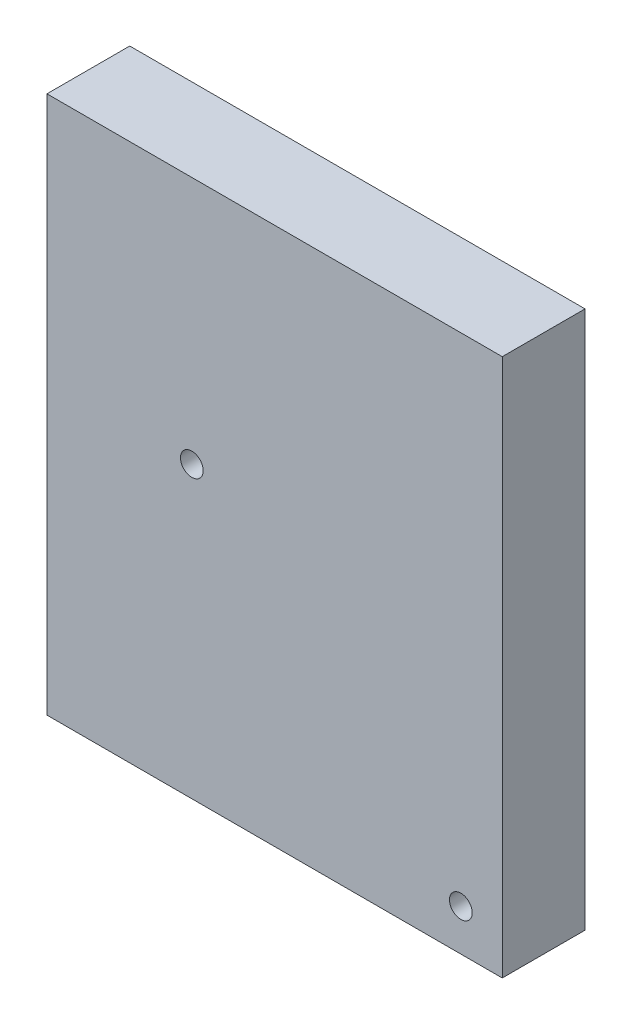
SolidWorks part; units mm, degrees
ref_plane "Front Plane" through (0, 0, 0) normal (0, 0, 1) x (1, 0, 0)
ref_plane "Top Plane" through (0, 0, 0) normal (0, 1, 0) x (1, 0, 0)
ref_plane "Right Plane" through (0, 0, 0) normal (1, 0, 0) x (0, 0, -1)
sketch "Sketch1" plane through (0, 0, 0) normal (0, 0, 1) x (1, 0, 0)
  line L1 (-27.94, -33.02) -> (27.94, -33.02)
  line L2 (-27.94, -33.02) -> (-27.94, 33.02)
  line L3 (-27.94, 33.02) -> (27.94, 33.02)
  line L4 (27.94, -33.02) -> (27.94, 33.02)
  line L5 (-27.94, -33.02) -> (27.94, 33.02) construction
  line L6 (-27.94, 33.02) -> (27.94, -33.02) construction
  circle A0 centre (-10.16, 2.54) radius 1.397
  circle A1 centre (22.86, -27.94) radius 1.397
  point P0 (0, 0)
  dimension "D3" = 2.794
  dimension "D4" = 2.794
  dimension "D1" = 55.88
  dimension "D2" = 66.04
  dimension "D5" = 5.08
  dimension "D6" = 50.8
  dimension "D7" = 17.78
  dimension "D8" = 35.56
extrude "Boss-Extrude1" add sketch "Sketch1" along normal blind 10.16
